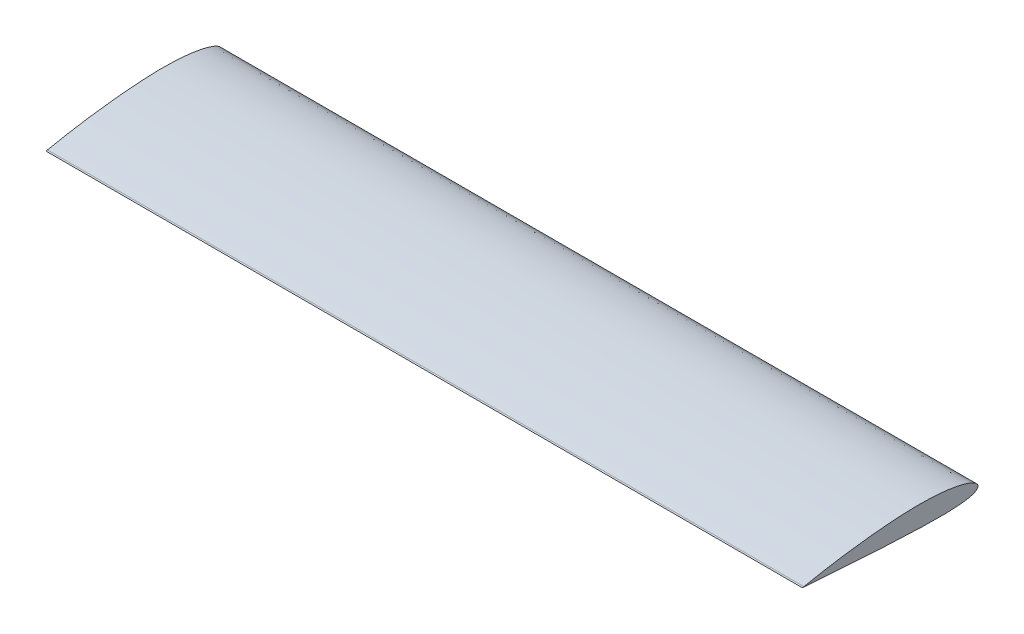
SolidWorks part; units mm, degrees
ref_plane "Front Plane" through (0, 0, 0) normal (0, 0, 1) x (1, 0, 0)
ref_plane "Top Plane" through (0, 0, 0) normal (0, 1, 0) x (1, 0, 0)
ref_plane "Right Plane" through (0, 0, 0) normal (1, 0, 0) x (0, 0, -1)
curve "Curve4"
  spline degree 3 poles (0, 0.5782, 460.0386) (0, 0.627, 459.8045) (0, 0.8218, 458.8693) (0, 1.2575, 456.7702) (0, 1.9746, 453.2853) (0, 2.9589, 448.4343) (0, 4.1943, 442.246) (0, 5.6576, 434.756) (0, 7.3237, 426.0083) (0, 9.1654, 416.0545) (0, 11.1514, 404.9531) (0, 13.2508, 392.7705) (0, 15.4318, 379.5792) (0, 17.6608, 365.4584) (0, 19.9051, 350.4932) (0, 22.1324, 334.7747) (0, 24.3093, 318.3983) (0, 26.4036, 301.4642) (0, 28.3853, 284.0765) (0, 30.2198, 266.3421) (0, 31.8805, 248.3712) (0, 33.3337, 230.2752) (0, 34.5557, 212.1676) (0, 35.5177, 194.1411) (0, 36.2071, 176.2823) (0, 36.4971, 158.7011) (0, 36.3855, 141.5343) (0, 35.8697, 124.9213) (0, 34.9559, 108.9721) (0, 33.6577, 93.7922) (0, 31.9979, 79.4811) (0, 30.0045, 66.1324) (0, 27.7126, 53.8316) (0, 25.1612, 42.6566) (0, 22.3959, 32.6749) (0, 19.4595, 23.9454) (0, 16.3987, 16.5145) (0, 13.2541, 10.4166) (0, 10.057, 5.6671) (0, 6.814, 2.2686) (0, 3.4608, 0.2233) (0, -0.0263, -0.2623) (0, -3.3451, 0.9027) (0, -6.2305, 3.5501) (0, -8.7569, 7.4782) (0, -11.0065, 12.6856) (0, -12.9908, 19.1637) (0, -14.712, 26.8853) (0, -16.1657, 35.8082) (0, -17.3506, 45.8799) (0, -18.2687, 57.0399) (0, -18.9276, 69.2218) (0, -19.3379, 82.3538) (0, -19.5167, 96.3593) (0, -19.4833, 111.1577) (0, -19.2643, 126.6644) (0, -18.8863, 142.7909) (0, -18.3822, 159.4455) (0, -17.7784, 176.5596) (0, -17.1172, 194.0554) (0, -16.3175, 211.825) (0, -15.4195, 229.7352) (0, -14.4427, 247.6567) (0, -13.4149, 265.4808) (0, -12.3547, 283.0986) (0, -11.2828, 300.4021) (0, -10.213, 317.2845) (0, -9.1604, 333.6415) (0, -8.1361, 349.3714) (0, -7.1489, 364.3761) (0, -6.2079, 378.5613) (0, -5.318, 391.8378) (0, -4.4882, 404.1215) (0, -3.7225, 415.3344) (0, -3.0283, 425.4049) (0, -2.4106, 434.2684) (0, -1.8753, 441.868) (0, -1.429, 448.1545) (0, -1.0753, 453.087) (0, -0.8201, 456.6335) (0, -0.6648, 458.7706) (0, -0.5955, 459.7229) (0, -0.5782, 459.9614) knots 0 0 0 0 0.000764 0.003052 0.00685 0.012132 0.018868 0.027013 0.036517 0.047321 0.059357 0.072551 0.08682 0.102077 0.118228 0.135171 0.152802 0.171013 0.18969 0.208718 0.227979 0.247354 0.266723 0.285966 0.305032 0.323824 0.342144 0.35988 0.376926 0.393182 0.408553 0.422951 0.436298 0.448523 0.459565 0.469379 0.477934 0.48522 0.491268 0.496168 0.500133 0.503587 0.507041 0.511 0.515876 0.521872 0.529071 0.537495 0.547131 0.557945 0.56989 0.582904 0.596922 0.611866 0.627656 0.644204 0.661417 0.679197 0.697443 0.716134 0.735139 0.754278 0.773432 0.792487 0.811323 0.829826 0.84788 0.865374 0.882198 0.898247 0.913421 0.927622 0.940763 0.952759 0.963533 0.973016 0.981148 0.987875 0.993154 0.996949 0.999236 1 1 1 1
sketch "Sketch4" plane through (0, 0, 0) normal (1, 0, 0) x (0, 0, -1)
  line L0 (0, 0) -> (-464.061, 0) construction
  line L1 (-460.0386, 0.5782) -> (-464.061, -0.2597)
  line L2 (-459.9614, -0.5782) -> (-464.061, -0.2597)
  spline S0 degree 3 poles (-1114.0421, 1884.4113) (-625.8801, -39.6264) (-542.4843, -16.5331) (-456.7702, 1.2575) (-453.2853, 1.9746) (-448.4343, 2.9589) (-442.246, 4.1943) (-434.756, 5.6576) (-426.0083, 7.3237) (-416.0545, 9.1654) (-404.9531, 11.1514) (-392.7705, 13.2508) (-379.5792, 15.4318) (-365.4584, 17.6608) (-350.4932, 19.9051) (-334.7747, 22.1324) (-318.3983, 24.3093) (-301.4642, 26.4036) (-284.0765, 28.3853) (-266.3421, 30.2198) (-248.3712, 31.8805) (-230.2752, 33.3337) (-212.1676, 34.5557) (-194.1411, 35.5177) (-176.2823, 36.2071) (-158.7011, 36.4971) (-141.5343, 36.3855) (-124.9213, 35.8697) (-108.9721, 34.9559) (-93.7922, 33.6577) (-79.4811, 31.9979) (-66.1324, 30.0045) (-53.8316, 27.7126) (-42.6566, 25.1612) (-32.6749, 22.3959) (-23.9454, 19.4595) (-16.5145, 16.3987) (-10.4166, 13.2541) (-5.6671, 10.057) (-2.2686, 6.814) (-0.2233, 3.4608) (0.2623, -0.0263) (-0.9027, -3.3451) (-3.5501, -6.2305) (-7.4782, -8.7569) (-12.6856, -11.0065) (-19.1637, -12.9908) (-26.8853, -14.712) (-35.8082, -16.1657) (-45.8799, -17.3506) (-57.0399, -18.2687) (-69.2218, -18.9276) (-82.3538, -19.3379) (-96.3593, -19.5167) (-111.1577, -19.4833) (-126.6644, -19.2643) (-142.7909, -18.8863) (-159.4455, -18.3822) (-176.5596, -17.7784) (-194.0554, -17.1172) (-211.825, -16.3175) (-229.7352, -15.4195) (-247.6567, -14.4427) (-265.4808, -13.4149) (-283.0986, -12.3547) (-300.4021, -11.2828) (-317.2845, -10.213) (-333.6415, -9.1604) (-349.3714, -8.1361) (-364.3761, -7.1489) (-378.5613, -6.2079) (-391.8378, -5.318) (-404.1215, -4.4882) (-415.3344, -3.7225) (-425.4049, -3.0283) (-434.2684, -2.4106) (-441.868, -1.8753) (-448.1545, -1.429) (-453.087, -1.0753) (-456.6335, -0.8201) (-717.3111, 18.1287) (-976.9217, 35.3368) (-1108.8718, 1836.6164) knots -0.27286 -0.27286 -0.27286 -0.27286 0.000764 0.003052 0.00685 0.012132 0.018868 0.027013 0.036517 0.047321 0.059357 0.072551 0.08682 0.102077 0.118228 0.135171 0.152802 0.171013 0.18969 0.208718 0.227979 0.247354 0.266723 0.285966 0.305032 0.323824 0.342144 0.35988 0.376926 0.393182 0.408553 0.422951 0.436298 0.448523 0.459565 0.469379 0.477934 0.48522 0.491268 0.496168 0.500133 0.503587 0.507041 0.511 0.515876 0.521872 0.529071 0.537495 0.547131 0.557945 0.56989 0.582904 0.596922 0.611866 0.627656 0.644204 0.661417 0.679197 0.697443 0.716134 0.735139 0.754278 0.773432 0.792487 0.811323 0.829826 0.84788 0.865374 0.882198 0.898247 0.913421 0.927622 0.940763 0.952759 0.963533 0.973016 0.981148 0.987875 0.993154 0.996949 0.999236 1.828266 1.828266 1.828266 1.828266 only from (-460.0386, 0.5782) to (-459.9614, -0.5782) construction
  spline S1 degree 3 poles (-460.0386, 0.5782) (-459.8045, 0.627) (-458.8693, 0.8218) (-456.7702, 1.2575) (-453.2853, 1.9746) (-448.4343, 2.9589) (-442.246, 4.1943) (-434.756, 5.6576) (-426.0083, 7.3237) (-416.0545, 9.1654) (-404.9531, 11.1514) (-392.7705, 13.2508) (-379.5792, 15.4318) (-365.4584, 17.6608) (-350.4932, 19.9051) (-334.7747, 22.1324) (-318.3983, 24.3093) (-301.4642, 26.4036) (-284.0765, 28.3853) (-266.3421, 30.2198) (-248.3712, 31.8805) (-230.2752, 33.3337) (-212.1676, 34.5557) (-194.1411, 35.5177) (-176.2823, 36.2071) (-158.7011, 36.4971) (-141.5343, 36.3855) (-124.9213, 35.8697) (-108.9721, 34.9559) (-93.7922, 33.6577) (-79.4811, 31.9979) (-66.1324, 30.0045) (-53.8316, 27.7126) (-42.6566, 25.1612) (-32.6749, 22.3959) (-23.9454, 19.4595) (-16.5145, 16.3987) (-10.4166, 13.2541) (-5.6671, 10.057) (-2.2686, 6.814) (-0.2233, 3.4608) (0.2623, -0.0263) (-0.9027, -3.3451) (-3.5501, -6.2305) (-7.4782, -8.7569) (-12.6856, -11.0065) (-19.1637, -12.9908) (-26.8853, -14.712) (-35.8082, -16.1657) (-45.8799, -17.3506) (-57.0399, -18.2687) (-69.2218, -18.9276) (-82.3538, -19.3379) (-96.3593, -19.5167) (-111.1577, -19.4833) (-126.6644, -19.2643) (-142.7909, -18.8863) (-159.4455, -18.3822) (-176.5596, -17.7784) (-194.0554, -17.1172) (-211.825, -16.3175) (-229.7352, -15.4195) (-247.6567, -14.4427) (-265.4808, -13.4149) (-283.0986, -12.3547) (-300.4021, -11.2828) (-317.2845, -10.213) (-333.6415, -9.1604) (-349.3714, -8.1361) (-364.3761, -7.1489) (-378.5613, -6.2079) (-391.8378, -5.318) (-404.1215, -4.4882) (-415.3344, -3.7225) (-425.4049, -3.0283) (-434.2684, -2.4106) (-441.868, -1.8753) (-448.1545, -1.429) (-453.087, -1.0753) (-456.6335, -0.8201) (-458.7706, -0.6648) (-459.7229, -0.5955) (-459.9614, -0.5782) knots 0 0 0 0 0.000764 0.003052 0.00685 0.012132 0.018868 0.027013 0.036517 0.047321 0.059357 0.072551 0.08682 0.102077 0.118228 0.135171 0.152802 0.171013 0.18969 0.208718 0.227979 0.247354 0.266723 0.285966 0.305032 0.323824 0.342144 0.35988 0.376926 0.393182 0.408553 0.422951 0.436298 0.448523 0.459565 0.469379 0.477934 0.48522 0.491268 0.496168 0.500133 0.503587 0.507041 0.511 0.515876 0.521872 0.529071 0.537495 0.547131 0.557945 0.56989 0.582904 0.596922 0.611866 0.627656 0.644204 0.661417 0.679197 0.697443 0.716134 0.735139 0.754278 0.773432 0.792487 0.811323 0.829826 0.84788 0.865374 0.882198 0.898247 0.913421 0.927622 0.940763 0.952759 0.963533 0.973016 0.981148 0.987875 0.993154 0.996949 0.999236 1 1 1 1
extrude "Boss-Extrude1" add sketch "Sketch4" along normal mid plane 2000
